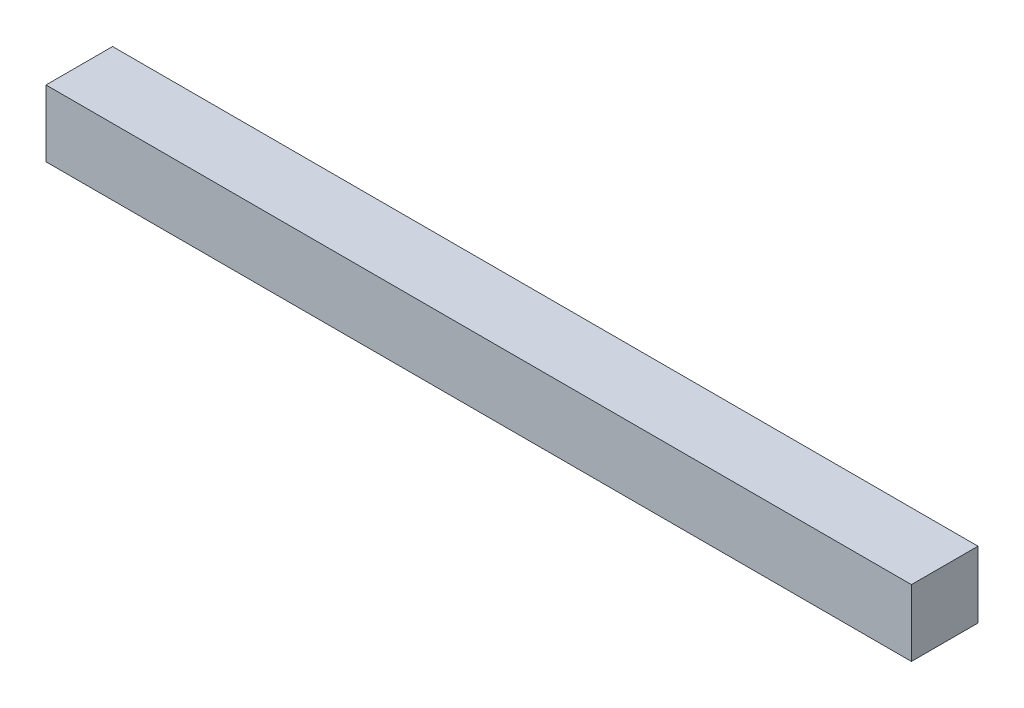
SolidWorks part; units mm, degrees
ref_plane "Front Plane" through (0, 0, 0) normal (0, 0, 1) x (1, 0, 0)
ref_plane "Top Plane" through (0, 0, 0) normal (0, 1, 0) x (1, 0, 0)
ref_plane "Right Plane" through (0, 0, 0) normal (1, 0, 0) x (0, 0, -1)
sketch "Sketch1" plane through (0, 0, 0) normal (0, 1, 0) x (1, 0, 0)
  line L1 (-165.1, -12.7) -> (165.1, -12.7)
  line L2 (-165.1, -12.7) -> (-165.1, 12.7)
  line L3 (-165.1, 12.7) -> (165.1, 12.7)
  line L4 (165.1, -12.7) -> (165.1, 12.7)
  line L5 (-165.1, -12.7) -> (165.1, 12.7) construction
  line L6 (-165.1, 12.7) -> (165.1, -12.7) construction
  point P0 (0, 0)
  dimension "D1" = 25.4
  dimension "D2" = 330.2
extrude "Boss-Extrude1" add sketch "Sketch1" along normal blind 25.4
